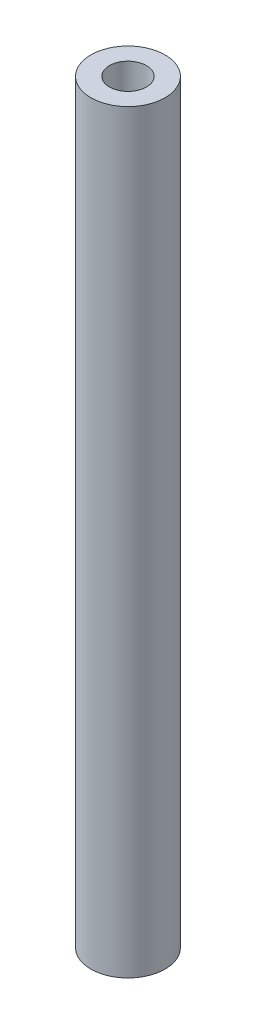
SolidWorks part; units mm, degrees
ref_plane "Front Plane" through (0, 0, 0) normal (0, 0, 1) x (1, 0, 0)
ref_plane "Top Plane" through (0, 0, 0) normal (0, 1, 0) x (1, 0, 0)
ref_plane "Right Plane" through (0, 0, 0) normal (1, 0, 0) x (0, 0, -1)
sketch "Sketch1" plane through (0, 0, 0) normal (0, 1, 0) x (1, 0, 0)
  circle A0 centre (0, 0) radius 1.5
  circle A1 centre (0, 0) radius 3
  dimension "D1" = 6
  dimension "D2" = 3
extrude "Boss-Extrude1" add sketch "Sketch1" along normal blind 61
